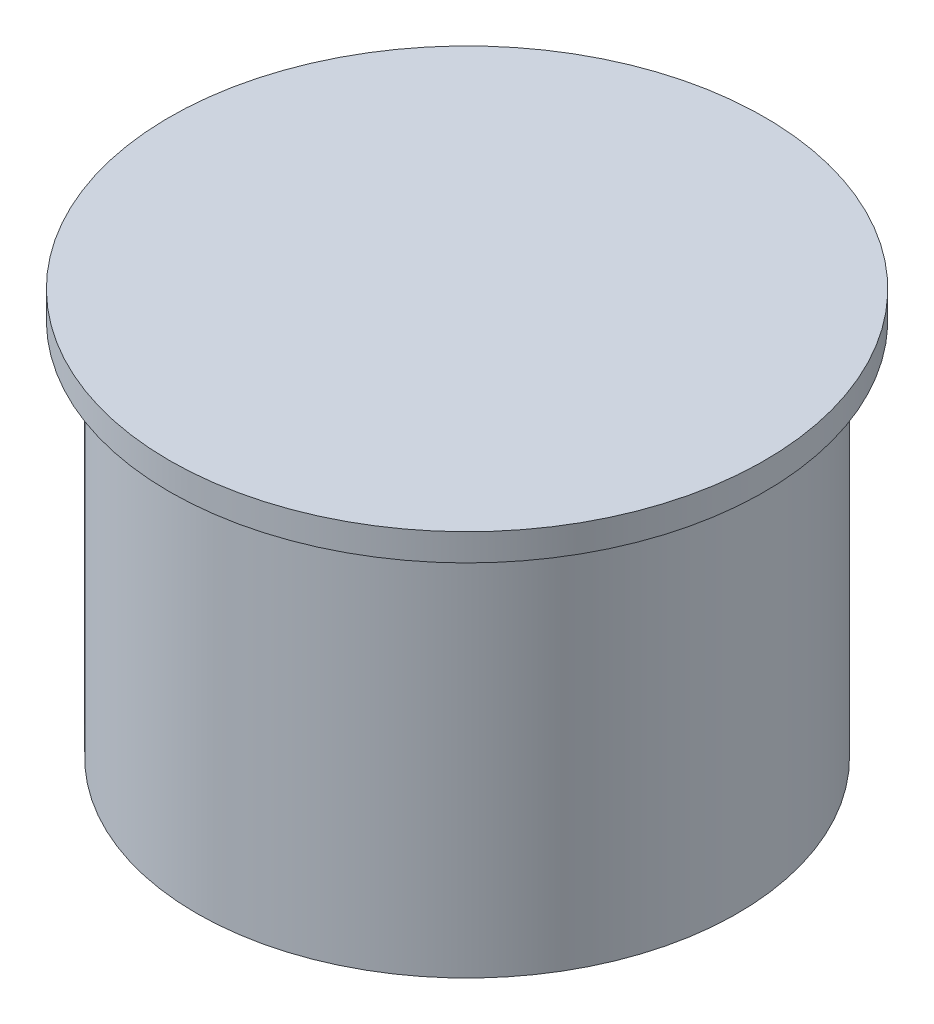
SolidWorks part; units mm, degrees
ref_plane "Front Plane" through (0, 0, 0) normal (0, 0, 1) x (1, 0, 0)
ref_plane "Top Plane" through (0, 0, 0) normal (0, 1, 0) x (1, 0, 0)
ref_plane "Right Plane" through (0, 0, 0) normal (1, 0, 0) x (0, 0, -1)
sketch "Sketch1" plane through (0, 0, 0) normal (1, 0, 0) x (0, 0, -1)
  line L0 (0, 0) -> (50, 0)
  line L1 (50, 0) -> (50, 70)
  line L2 (50, 70) -> (55, 70)
  line L3 (55, 70) -> (55, 75)
  line L4 (55, 75) -> (0, 75)
  line L5 (0, 75) -> (0, 0)
  dimension "D1" = 75
  dimension "D2" = 5
  dimension "D3" = 5
  dimension "D4" = 55
revolve "Revolve1" add sketch "Sketch1" angle 360 about L5
sketch "Sketch2" plane through (0, 0, 0) normal (0, -1, 0) x (1, 0, 0)
  line L1 (-24.7487, -24.7487) -> (24.7487, -24.7487) construction
  line L2 (-24.7487, -24.7487) -> (-24.7487, 24.7487) construction
  line L3 (-24.7487, 24.7487) -> (24.7487, 24.7487) construction
  line L4 (24.7487, -24.7487) -> (24.7487, 24.7487) construction
  line L5 (-24.7487, -24.7487) -> (24.7487, 24.7487) construction
  line L6 (-24.7487, 24.7487) -> (24.7487, -24.7487) construction
  circle A0 centre (-24.7487, 24.7487) radius 4
  circle A1 centre (24.7487, 24.7487) radius 4
  circle A2 centre (24.7487, -24.7487) radius 4
  circle A3 centre (-24.7487, -24.7487) radius 4
  point P0 (0, 0)
  dimension "D2" = 8
  dimension "D1" = 70
extrude "Cut-Extrude1" cut sketch "Sketch2" against normal blind 30
